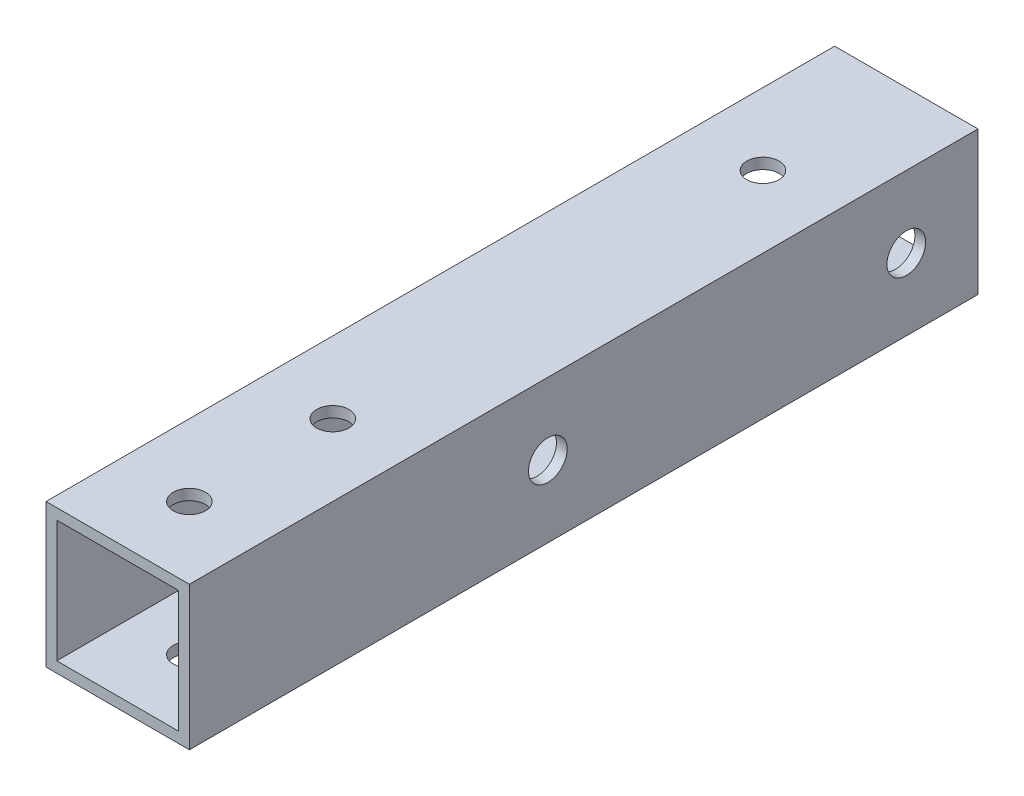
SolidWorks part; units mm, degrees
material "1060 合金"
ref_plane "正面" through (0, 0, 0) normal (0, 0, 1) x (1, 0, 0)
ref_plane "平面" through (0, 0, 0) normal (0, 1, 0) x (1, 0, 0)
ref_plane "右側面" through (0, 0, 0) normal (1, 0, 0) x (0, 0, -1)
sketch "ｽｹｯﾁ1" plane through (0, 0, 0) normal (0, 0, 1) x (1, 0, 0)
  line L1 (-10, -10) -> (10, -10)
  line L2 (-10, -10) -> (-10, 10)
  line L3 (-10, 10) -> (10, 10)
  line L4 (10, -10) -> (10, 10)
  line L5 (-10, -10) -> (10, 10) construction
  line L6 (-10, 10) -> (10, -10) construction
  line L7 (-8.5, -8.5) -> (8.5, -8.5)
  line L8 (-8.5, -8.5) -> (-8.5, 8.5)
  line L9 (-8.5, 8.5) -> (8.5, 8.5)
  line L10 (8.5, -8.5) -> (8.5, 8.5)
  line L11 (-8.5, -8.5) -> (8.5, 8.5) construction
  line L12 (-8.5, 8.5) -> (8.5, -8.5) construction
  point P0 (0, 0)
  point P6 (0, 0)
  dimension "D1" = 1.5
  dimension "D2" = 20
  dimension "D3" = 20
extrude "ﾎﾞｽ - 押し出し1" add sketch "ｽｹｯﾁ1" along normal blind 110
sketch "ｽｹｯﾁ2" plane through (10, 0, 0) normal (1, 0, 0) x (0, 0, -1)
  line L0 (-110, -10) -> (0, -10) construction
  circle A9 centre (-60, 0) radius 2.7
  circle A10 centre (-10, 0) radius 2.7
  dimension "D1" = 50
  dimension "D6" = 5.4
  dimension "D8" = 5.4
  dimension "D4" = 10
  dimension "D5" = 10
  dimension "D9" = 10
extrude "ｶｯﾄ - 押し出し1" cut sketch "ｽｹｯﾁ2" against normal blind 25
sketch "ｽｹｯﾁ3" plane through (0, 10, 0) normal (0, 1, 0) x (1, 0, 0)
  line L0 (10, -110) -> (-10, -110) construction
  line L1 (-10, -110) -> (-10, 0) construction
  circle A0 centre (0, -100) radius 2.25
  circle A4 centre (0, -80) radius 2.25
  circle A5 centre (0, -20) radius 2.25
  dimension "D1" = 4.5
  dimension "D2" = 10
  dimension "D3" = 10
  dimension "D6" = 2
  dimension "D7" = 20
  dimension "D5" = 20
  dimension "D4" = 2
extrude "ｶｯﾄ - 押し出し2" cut sketch "ｽｹｯﾁ3" against normal blind 20
sketch "ｽｹｯﾁ5" plane through (0, -10, 0) normal (0, -1, 0) x (-1, 0, 0)
  circle A0 centre (0, -20) radius 5
  dimension "D1" = 10
extrude "ｶｯﾄ - 押し出し4" cut sketch "ｽｹｯﾁ5" against normal blind 10
sketch "ｽｹｯﾁ6" plane through (-10, 0, 0) normal (-1, 0, 0) x (0, 0, 1)
  circle A0 centre (10, 0) radius 5
  circle A1 centre (60, 0) radius 5
  dimension "D1" = 10
  dimension "D2" = 10
extrude "ｶｯﾄ - 押し出し5" cut sketch "ｽｹｯﾁ6" against normal blind 10
